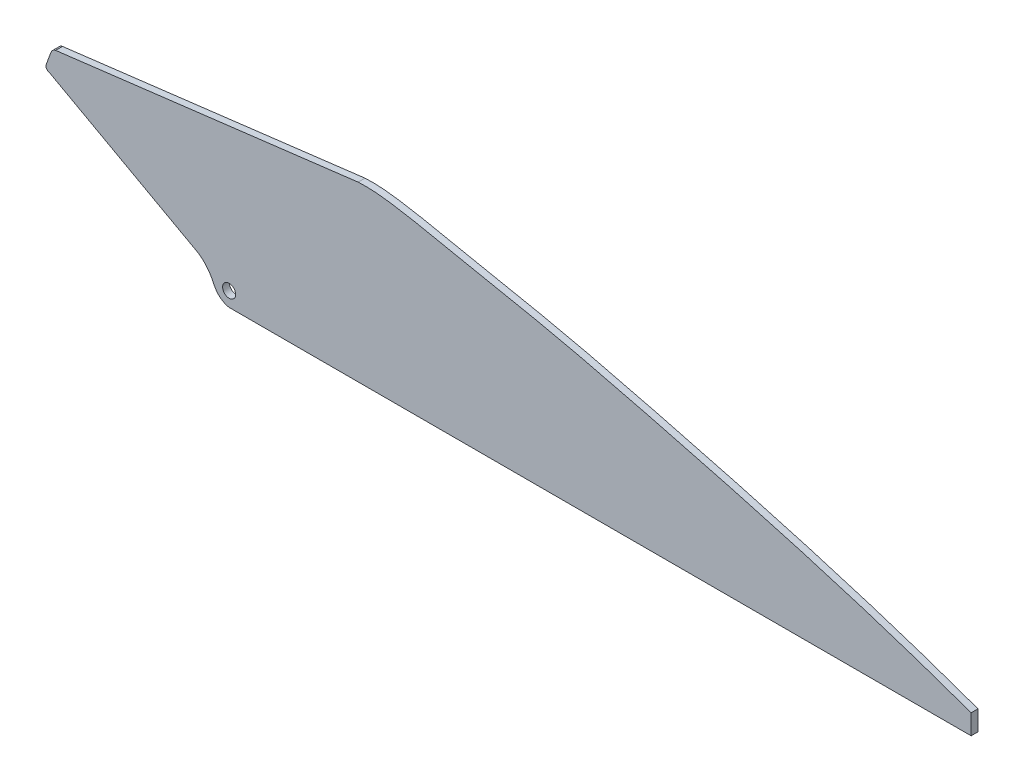
SolidWorks part; units mm, degrees
material "6061-T6 (SS)"
ref_plane "Front Plane" through (0, 0, 0) normal (0, 0, 1) x (1, 0, 0)
ref_plane "Top Plane" through (0, 0, 0) normal (0, 1, 0) x (1, 0, 0)
ref_plane "Right Plane" through (0, 0, 0) normal (1, 0, 0) x (0, 0, -1)
sketch "Sketch1" plane through (0, 0, 0) normal (0, 0, 1) x (1, 0, 0)
  line L0 (1020.9901, -1754.1208) -> (-399.4151, -3402.5822) construction
  line L1 (7.8634, -33.8695) -> (715.8884, -33.8695)
  line L2 (715.8884, -33.8695) -> (715.8884, -14.8195)
  line L3 (-163.2254, 74.2452) -> (-21.7609, -3.4928)
  line L4 (-166.0074, 81.4482) -> (-162.0453, 92.076)
  line L5 (-157.6612, 95.7715) -> (130.9232, 131.2305)
  circle A0 centre (7.8634, -20.0818) radius 6.223
  spline S0 degree 3 poles (-21.7609, -3.4928) (-15.524, -7.5897) (-9.8334, -14.7208) (-4.0175, -28.0233) (2.0811, -32.9022) (7.8634, -33.8695) knots 0 0 0 0 0.506293 0.611828 1 1 1 1
  spline S1 degree 2 poles (-166.0074, 81.4482) (-168.609, 75.8607) (-163.2254, 74.2452) knots 0 0 0 1 1 1
  spline S2 degree 2 poles (-162.0453, 92.076) (-160.7914, 95.0159) (-157.6612, 95.7715) knots 0 0 0 1 1 1
  spline S3 degree 3 poles (130.9232, 131.2305) (144.5652, 132.0326) (175.7455, 127.8597) (235.9798, 114.8515) (312.7915, 100.52) (477.9357, 59.8555) (612.6955, 22.7299) (715.8884, -14.8195) knots 0 0 0 0 0.067559 0.155585 0.30617 0.455389 1 1 1 1
extrude "Boss-Extrude1" add sketch "Sketch1" along normal blind 6.5532
